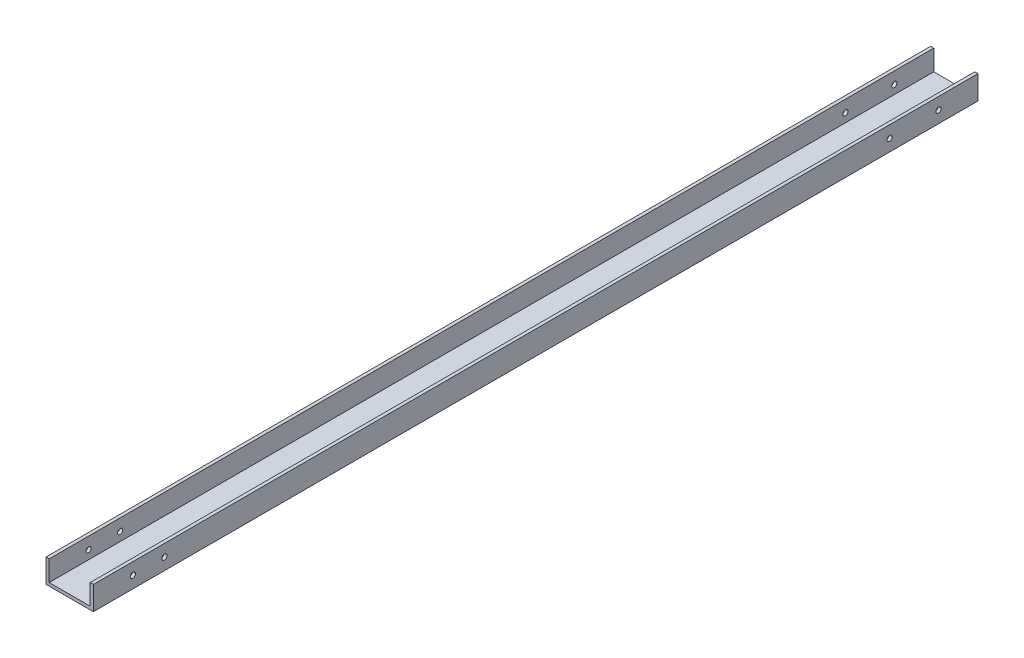
SolidWorks part; units mm, degrees
ref_plane "正面" through (0, 0, 0) normal (0, 0, 1) x (1, 0, 0)
ref_plane "平面" through (0, 0, 0) normal (0, 1, 0) x (1, 0, 0)
ref_plane "右側面" through (0, 0, 0) normal (1, 0, 0) x (0, 0, -1)
sketch "ｽｹｯﾁ1" plane through (0, 0, 0) normal (0, 0, 1) x (1, 0, 0)
  line L0 (0, 0) -> (15, 0)
  line L1 (0, 0) -> (-15, 0)
  line L2 (-15, 0) -> (-15, 15)
  line L3 (15, 0) -> (15, 15)
  line L4 (-15, 15) -> (-13, 15)
  line L5 (15, 15) -> (13, 15)
  line L6 (-13, 15) -> (-13, 2)
  line L7 (13, 15) -> (13, 2)
  line L8 (-13, 2) -> (13, 2)
  dimension "D1" = 15
  dimension "D2" = 15
  dimension "D3" = 15
  dimension "D4" = 15
  dimension "D5" = 2
  dimension "D6" = 2
  dimension "D7" = 13
  dimension "D8" = 13
extrude "ﾎﾞｽ - 押し出し1" add sketch "ｽｹｯﾁ1" along normal blind 560.3
sketch "ｽｹｯﾁ4" plane through (15, 0, 0) normal (1, 0, 0) x (0, 0, -1)
  line L0 (-560.3, 7.5) -> (-535.3, 7.5)
  line L1 (-560.3, 0) -> (-560.3, 15) construction
  line L2 (-560.3, 7.5) -> (-515.3, 7.5)
  circle A0 centre (-535.3, 7.5) radius 2.2
  circle A1 centre (-515.3, 7.5) radius 2.2
  dimension "D3" = 4.4
  dimension "D4" = 4.4
  dimension "D1" = 25
  dimension "D2" = 45
sketch "ｽｹｯﾁ5" plane through (15, 0, 0) normal (1, 0, 0) x (0, 0, -1)
  line L0 (0, 7.5) -> (-25, 7.5)
  line L1 (0, 0) -> (0, 15) construction
  line L2 (0, 7.5) -> (-56, 7.5)
  circle A0 centre (-25, 7.5) radius 2.2
  circle A1 centre (-56, 7.5) radius 2.2
  dimension "D3" = 4.4
  dimension "D4" = 4.4
  dimension "D1" = 25
  dimension "D2" = 56
sketch "ｽｹｯﾁ7" plane through (-15, 0, 0) normal (-1, 0, 0) x (0, 0, 1)
  line L1 (535.3, 7.5) -> (515.3, 7.5)
  line L2 (535.3, 7.5) -> (560.3, 7.5)
  line L3 (25, 7.5) -> (0, 7.5)
  line L4 (25, 7.5) -> (56, 7.5)
  circle A0 centre (25, 7.5) radius 2.2
  circle A1 centre (56, 7.5) radius 2.2
  circle A2 centre (515.3, 7.5) radius 2.2
  circle A3 centre (535.3, 7.5) radius 2.2
  dimension "D1" = 4.4
  dimension "D2" = 4.4
  dimension "D3" = 25
  dimension "D4" = 20
  dimension "D5" = 25
  dimension "D6" = 31
sketch "ｽｹｯﾁ8" plane through (15, 0, 0) normal (1, 0, 0) x (0, 0, -1)
  line L0 (0, 7.5) -> (-25, 7.5)
  line L1 (-25, 7.5) -> (-56, 7.5)
  circle A0 centre (-56, 7.5) radius 2.5943
  circle A1 centre (-25, 7.5) radius 2.9358
  dimension "D1" = 25
  dimension "D2" = 31
hole_wizard "M4x0.7 ねじ穴1" positions "3Dｽｹｯﾁ1" profile "ｽｹｯﾁ9" tap size "M4x0.7" standard "JIS"
sketch3d "3Dｽｹｯﾁ1"
  point P0 (15, 7.5, 56)
  point P3 (15, 7.5, 25)
sketch "ｽｹｯﾁ9" plane through (15, 7.5, 56) normal (0, 1, 0) x (0, 0, -1)
  line L0 (0, 0) -> (0, 12.4914)
  line L1 (0, 12.4914) -> (1.65, 11.5)
  line L2 (1.65, 11.5) -> (1.65, 0)
  line L5 (1.65, 0) -> (0, 0)
  line L10 (0, 12.4914) -> (-1.65, 11.5) construction
  line L11 (0, -6.35) -> (0, 107.95) construction
  dimension "ねじ下穴ﾄﾞﾘﾙ直径" = 3.3
  dimension "ねじ下穴ﾄﾞﾘﾙの深さ" = 11.5
  dimension "ﾄﾞﾘﾙ角度" = 118
cosmetic thread "穴のねじ山1" parameters "D1"=2, "D2"=4
cosmetic thread "穴のねじ山2" parameters "D1"=2, "D2"=4
hole_wizard "M4x0.7 ねじ穴2" positions "3Dｽｹｯﾁ2" profile "ｽｹｯﾁ10" tap size "M4x0.7" standard "JIS"
sketch3d "3Dｽｹｯﾁ2"
  point P0 (15, 7.5, 535.3)
  point P3 (15, 7.5, 515.3)
sketch "ｽｹｯﾁ10" plane through (15, 7.5, 535.3) normal (0, 1, 0) x (0, 0, -1)
  line L0 (0, 0) -> (0, 12.4914)
  line L1 (0, 12.4914) -> (1.65, 11.5)
  line L2 (1.65, 11.5) -> (1.65, 0)
  line L5 (1.65, 0) -> (0, 0)
  line L10 (0, 12.4914) -> (-1.65, 11.5) construction
  line L11 (0, -6.35) -> (0, 107.95) construction
  dimension "ねじ下穴ﾄﾞﾘﾙ直径" = 3.3
  dimension "ねじ下穴ﾄﾞﾘﾙの深さ" = 11.5
  dimension "ﾄﾞﾘﾙ角度" = 118
cosmetic thread "穴のねじ山3" parameters "D1"=2, "D2"=4
cosmetic thread "穴のねじ山4" parameters "D1"=2, "D2"=4
hole_wizard "M4x0.7 ねじ穴4" positions "3Dｽｹｯﾁ4" profile "ｽｹｯﾁ12" tap size "M4x0.7" standard "JIS"
sketch3d "3Dｽｹｯﾁ4"
  point P0 (-15, 7.5, 56)
  point P3 (-15, 7.5, 25)
  point P6 (-15, 7.5, 515.3)
  point P9 (-15, 7.5, 535.3)
sketch "ｽｹｯﾁ12" plane through (-15, 7.5, 56) normal (0, 1, 0) x (0, 0, 1)
  line L0 (0, 0) -> (0, 12.4914)
  line L1 (0, 12.4914) -> (1.65, 11.5)
  line L2 (1.65, 11.5) -> (1.65, 0)
  line L5 (1.65, 0) -> (0, 0)
  line L10 (0, 12.4914) -> (-1.65, 11.5) construction
  line L11 (0, -6.35) -> (0, 107.95) construction
  dimension "ねじ下穴ﾄﾞﾘﾙ直径" = 3.3
  dimension "ねじ下穴ﾄﾞﾘﾙの深さ" = 11.5
  dimension "ﾄﾞﾘﾙ角度" = 118
cosmetic thread "穴のねじ山9" parameters "D1"=2, "D2"=4
cosmetic thread "穴のねじ山10" parameters "D1"=2, "D2"=4
cosmetic thread "穴のねじ山11" parameters "D1"=2, "D2"=4
cosmetic thread "穴のねじ山12" parameters "D1"=2, "D2"=4
